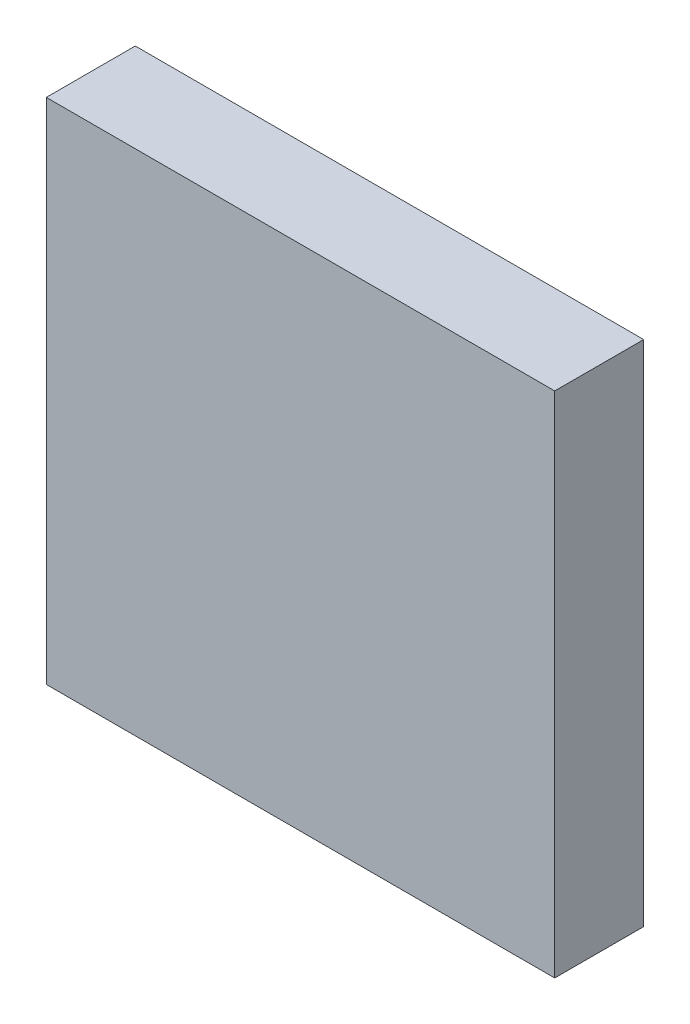
SolidWorks part; units mm, degrees
ref_plane "Front Plane" through (0, 0, 0) normal (0, 0, 1) x (1, 0, 0)
ref_plane "Top Plane" through (0, 0, 0) normal (0, 1, 0) x (1, 0, 0)
ref_plane "Right Plane" through (0, 0, 0) normal (1, 0, 0) x (0, 0, -1)
sketch "Sketch1" plane through (0, 0, 0) normal (0, 0, 1) x (1, 0, 0)
  line L0 (-1000, 1000) -> (1000, 1000)
  line L1 (-950, 950) -> (950, 950)
  line L2 (-950, 950) -> (-950, -950)
  line L3 (-950, -950) -> (950, -950)
  line L4 (950, 950) -> (950, -950)
  line L5 (-950, 950) -> (950, -950) construction
  line L6 (-950, -950) -> (950, 950) construction
  line L7 (1000, 1000) -> (1000, -1000)
  line L8 (-1000, -1000) -> (1000, -1000)
  line L9 (-1000, 1000) -> (-1000, -1000)
  line L10 (-950, 299.988) -> (-950, 249.988)
  line L11 (-950, 650) -> (950, 650)
  line L12 (-950, 650) -> (-950, 600)
  line L13 (-950, 600) -> (950, 600)
  line L14 (950, 650) -> (950, 600)
  line L15 (-950, 299.988) -> (950, 299.988)
  line L16 (950, 299.988) -> (950, 249.988)
  line L17 (-950, 249.988) -> (950, 249.988)
  line L18 (-950, -50.024) -> (-950, -100.024)
  line L19 (-950, -50.024) -> (950, -50.024)
  line L20 (950, -50.024) -> (950, -100.024)
  line L21 (-950, -100.024) -> (950, -100.024)
  line L22 (-950, -400.036) -> (-950, -450.036)
  line L23 (-950, -400.036) -> (950, -400.036)
  line L24 (950, -400.036) -> (950, -450.036)
  line L25 (-950, -450.036) -> (950, -450.036)
  line L26 (-950, -750.048) -> (-950, -800.048)
  line L27 (-950, -750.048) -> (950, -750.048)
  line L28 (950, -750.048) -> (950, -800.048)
  line L29 (-950, -800.048) -> (950, -800.048)
  point P0 (0, 0)
  dimension "D2" = 2000
  dimension "D3" = 2000
  dimension "D4" = 50
  dimension "D5" = 300
  dimension "D1" = 50
  dimension "D6" = 5
extrude "Boss-Extrude1" add sketch "Sketch1" along normal blind 300 contours L0 L9 L8 L7 L1 L4 L3 L2 | L2 L13 L4 L11 | L2 L17 L4 L15 | L2 L21 L4 L19 | L25 L24 L23 L22 | L29 L28 L27 L26
sketch "Sketch2" plane through (0, 0, 300) normal (0, 0, 1) x (1, 0, 0)
  line L4 (1000, 1000) -> (-1000, 1000)
  line L5 (-1000, 1000) -> (-1000, -1000)
  line L6 (-1000, -1000) -> (1000, -1000)
  line L7 (1000, -1000) -> (1000, 1000)
  line L8 (1000, 1000) -> (-1000, 1000)
  line L9 (-1000, 1000) -> (-1000, -1000)
  line L10 (-1000, -1000) -> (1000, -1000)
  line L11 (1000, -1000) -> (1000, 1000)
  dimension "D1" = 0
extrude "Boss-Extrude2" add sketch "Sketch2" along normal blind 50
